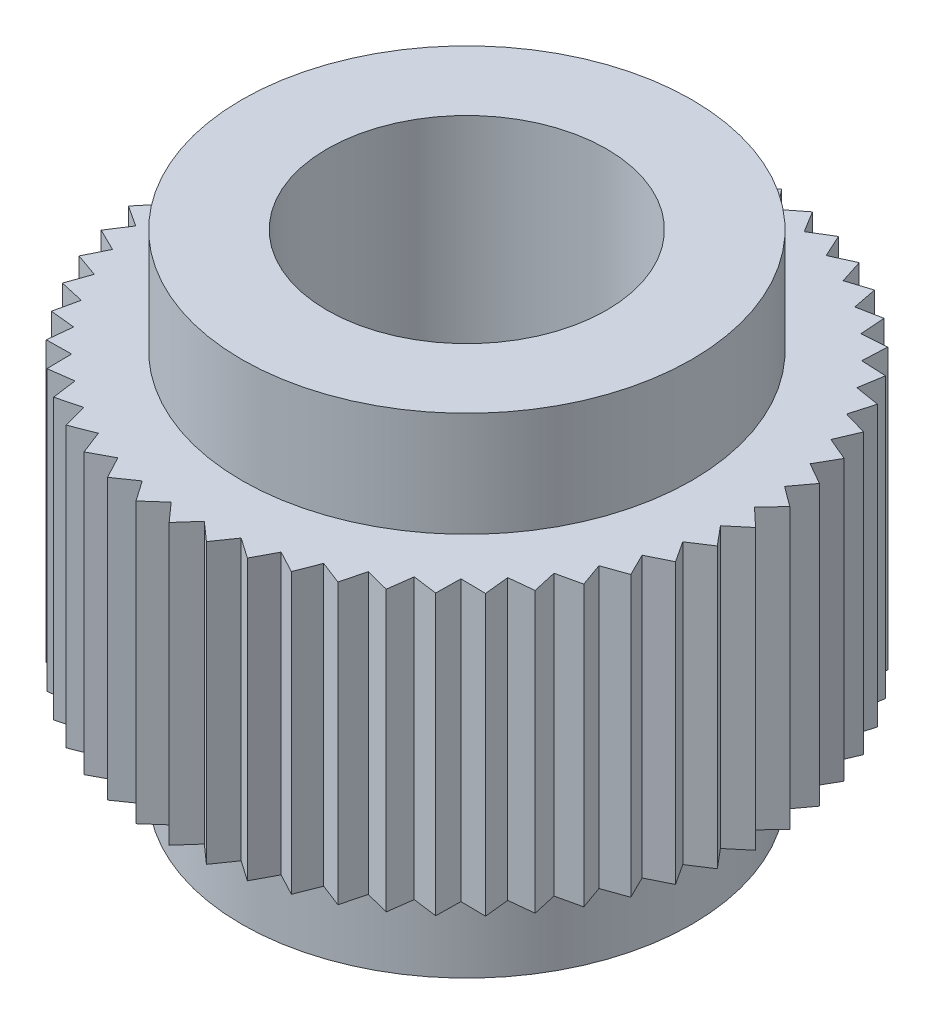
SolidWorks part; units mm, degrees
ref_plane "前视基准面" through (0, 0, 0) normal (0, 0, 1) x (1, 0, 0)
ref_plane "上视基准面" through (0, 0, 0) normal (0, 1, 0) x (1, 0, 0)
ref_plane "右视基准面" through (0, 0, 0) normal (1, 0, 0) x (0, 0, -1)
sketch "草图1" plane through (0, 0, 0) normal (0, 0, 1) x (1, 0, 0)
  line L0 (78.3483, 313.258) -> (391.7413, 313.258) construction
  line L1 (0, 0) -> (0, 50.7821) construction
  line L2 (0, 159.8289) -> (0, 127.4173) construction
  line L3 (0, 17) -> (4, 17)
  line L4 (4, 17) -> (4, 14)
  line L5 (4, 14) -> (6.44, 14)
  line L6 (6.44, 14) -> (6.44, 11)
  line L7 (6.44, 11) -> (9.5, 11)
  line L8 (9.5, 11) -> (9.5, 3)
  line L9 (9.5, 3) -> (6.44, 3)
  line L10 (6.44, 3) -> (6.44, 0)
  line L11 (6.44, 0) -> (0, 0)
  line L12 (0, 17) -> (0, 0)
  line L13 (0, 0) -> (32.9681, 0) construction
  dimension "D1" = 8
  dimension "D2" = 12.88
  dimension "D3" = 19
  dimension "D4" = 12.88
  dimension "D5" = 3
  dimension "D6" = 3
  dimension "D7" = 3
  dimension "D8" = 8
revolve "旋转1" add sketch "草图1" angle 360 about L12
sketch "草图2" plane through (0, 11, 0) normal (0, 1, 0) x (1, 0, 0)
  line L0 (0, 0) -> (0, 10.4548) construction
  line L1 (1.3968, 9.3968) -> (0, 8)
  line L2 (0, 8) -> (-1.3968, 9.3968)
  circle A1 centre (0, 0) radius 9.5 construction
  circle A2 centre (0, 0) radius 9.5
  circle A3 centre (0, 0) radius 8
  circle M2 centre (0, 0) radius 9.5
  dimension "D2" = 16
extrude "切除-拉伸2" cut sketch "草图2" against normal through all contours L2 L0 A2 | L0 L1 M2
pattern_circular "阵列(圆周)1" count 53 over 360 about axis through (0, 0, 0) along (0, 1, 0) of "切除-拉伸2"
sketch "草图3" plane through (0, 0, 0) normal (0, -1, 0) x (1, 0, 0)
  line L1 (3, -3) -> (-3, -3)
  line L2 (3, -3) -> (3, 3)
  line L3 (3, 3) -> (-3, 3)
  line L4 (-3, -3) -> (-3, 3)
  line L5 (3, -3) -> (-3, 3) construction
  line L6 (3, 3) -> (-3, -3) construction
  point P0 (0, 0)
  dimension "D1" = 6
  dimension "D2" = 6
sketch "草图4" plane through (0, 17, 0) normal (0, 1, 0) x (1, 0, 0)
  circle A0 centre (0, 0) radius 4 construction
  circle A1 centre (0, 0) radius 4
extrude "切除-拉伸3" cut sketch "草图4" against normal through all
